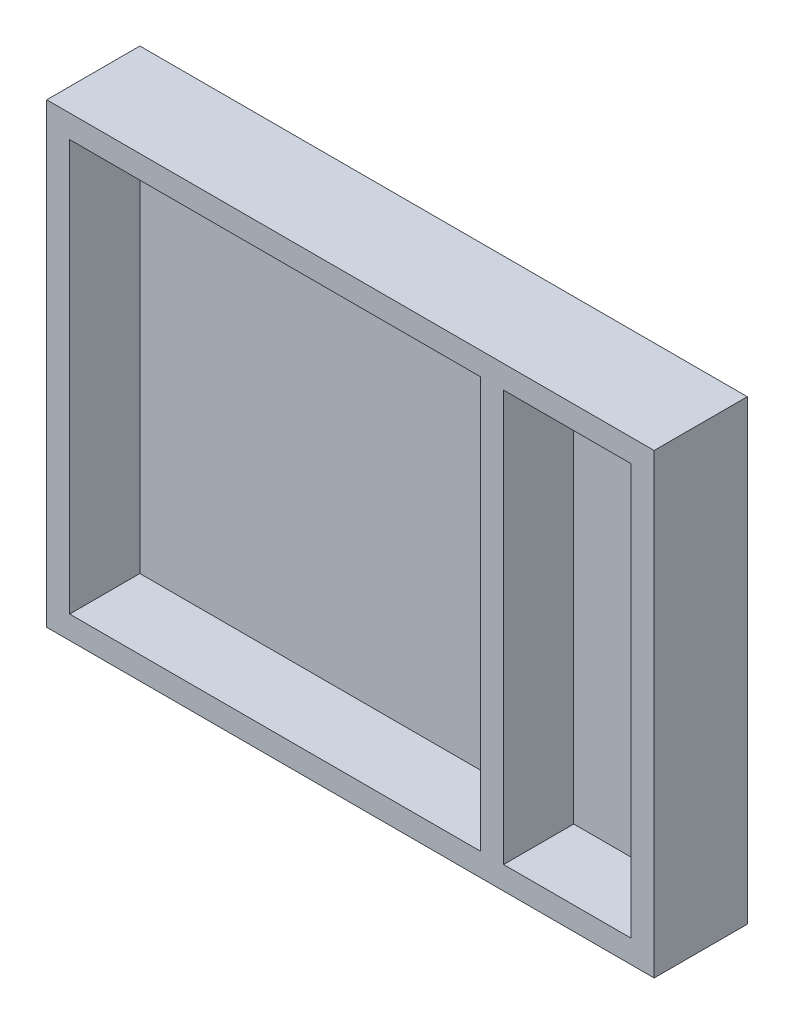
SolidWorks part; units mm, degrees
ref_plane "Front Plane" through (0, 0, 0) normal (0, 0, 1) x (1, 0, 0)
ref_plane "Top Plane" through (0, 0, 0) normal (0, 1, 0) x (1, 0, 0)
ref_plane "Right Plane" through (0, 0, 0) normal (1, 0, 0) x (0, 0, -1)
sketch "Sketch1" plane through (0, 0, 0) normal (0, 0, 1) x (1, 0, 0)
  line L0 (-18, -18) -> (340, -18)
  line L1 (0, 0) -> (322, 0)
  line L2 (0, 0) -> (0, 322)
  line L3 (0, 322) -> (322, 322)
  line L4 (322, 0) -> (322, 322)
  line L5 (340, 0) -> (340, 322)
  line L6 (-18, 340) -> (340, 340)
  line L7 (-18, -18) -> (-18, 340)
  line L8 (340, 322) -> (440, 322)
  line L9 (440, 322) -> (440, 0)
  line L10 (440, 0) -> (340, 0)
  line L11 (340, 340) -> (458, 340)
  line L12 (458, 340) -> (458, -18)
  line L13 (458, -18) -> (340, -18)
  line L15 (340, -18) -> (340, 340) construction
  dimension "D1" = 322
  dimension "D2" = 322
  dimension "D4" = 100
  dimension "D5" = 322
  dimension "D3" = 18
  dimension "D6" = 18
extrude "Boss-Extrude1" add sketch "Sketch1" along normal blind 55 contours L0 L15 L5 L6 L7 L4 L1 L2 L3 | L15 L13 L12 L11 L8 L9 L10
sketch "Sketch2" plane through (0, 0, 0) normal (0, 0, -1) x (-1, 0, 0)
  line L1 (-458, 340) -> (18, 340)
  line L2 (-458, 340) -> (-458, -18)
  line L3 (-458, -18) -> (18, -18)
  line L4 (18, 340) -> (18, -18)
extrude "Boss-Extrude2" add sketch "Sketch2" along normal blind 18
equation "\"D5@Sketch1\"=\"D2@Sketch1\""
